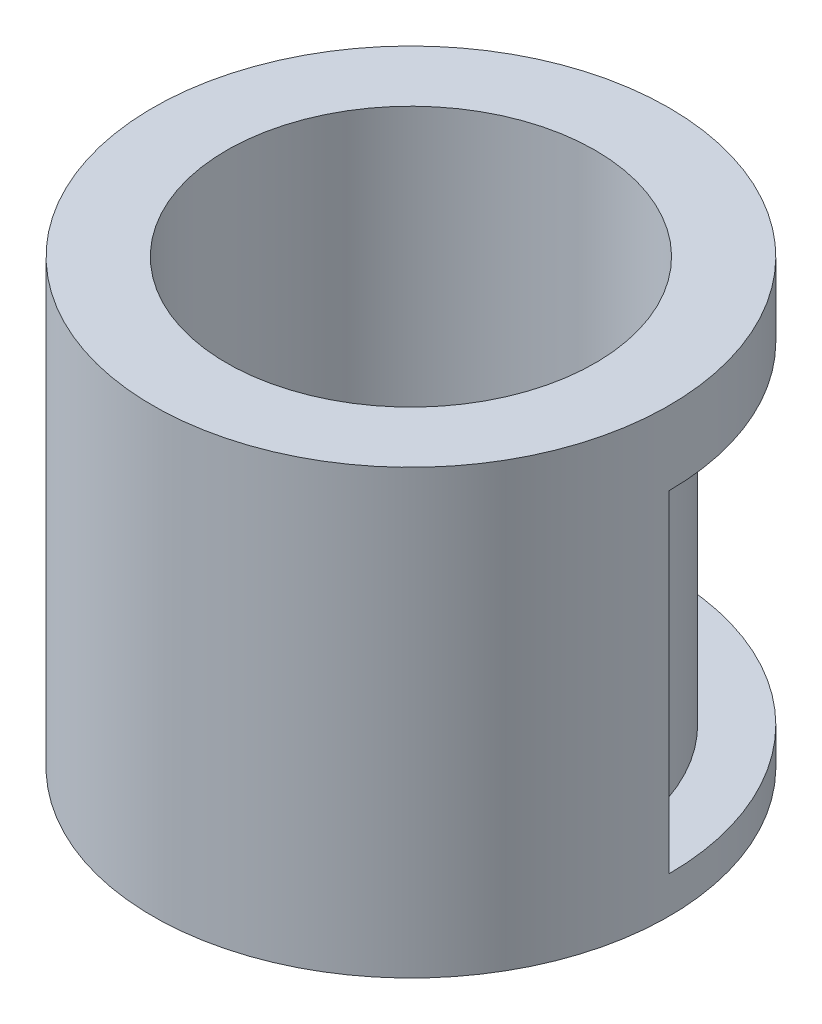
SolidWorks part; units mm, degrees
ref_plane "Front Plane" through (0, 0, 0) normal (0, 0, 1) x (1, 0, 0)
ref_plane "Top Plane" through (0, 0, 0) normal (0, 1, 0) x (1, 0, 0)
ref_plane "Right Plane" through (0, 0, 0) normal (1, 0, 0) x (0, 0, -1)
sketch "Sketch1" plane through (0, 0, 0) normal (0, 0, 1) x (1, 0, 0)
  line L0 (0, 0) -> (0, 127) construction
  line L1 (0, 0) -> (63.5, 0) construction
  line L2 (63.5, 0) -> (63.5, 152.4)
  line L3 (63.5, 152.4) -> (88.9, 152.4)
  line L4 (88.9, 152.4) -> (88.9, 0)
  line L5 (63.5, 0) -> (88.9, 0)
  dimension "D1" = 25.4
  dimension "D2" = 152.4
  dimension "D3" = 63.5
revolve "Revolve1" add sketch "Sketch1" angle 360 about L0
sketch "Sketch2" plane through (0, 0, 0) normal (0, 0, 1) x (1, 0, 0)
  line L0 (0, 0) -> (0, 12.7) construction
  line L1 (0, 12.7) -> (63.5, 12.7) construction
  line L2 (63.5, 12.7) -> (69.85, 12.7) construction
  line L3 (69.85, 12.7) -> (69.85, 127)
  line L4 (69.85, 127) -> (88.9, 127)
  line L5 (88.9, 0) -> (88.9, 152.4) construction
  line L6 (88.9, 127) -> (88.9, 12.7)
  line L7 (88.9, 12.7) -> (69.85, 12.7)
  dimension "D1" = 12.7
  dimension "D2" = 63.5
  dimension "D3" = 6.35
  dimension "D4" = 114.3
revolve "Cut-Revolve1" cut sketch "Sketch2" angle 120 about L0
